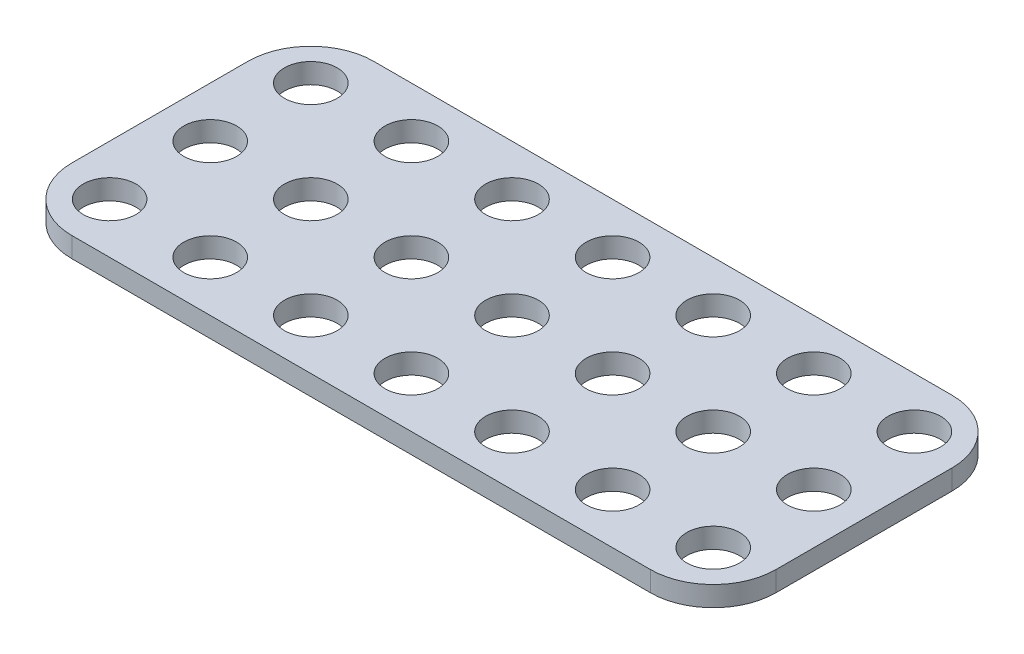
SolidWorks part; units mm, degrees
material "1060 Alloy"
ref_plane "Front Plane" through (0, 0, 0) normal (0, 0, 1) x (1, 0, 0)
ref_plane "Top Plane" through (0, 0, 0) normal (0, 1, 0) x (1, 0, 0)
ref_plane "Right Plane" through (0, 0, 0) normal (1, 0, 0) x (0, 0, -1)
sketch "Sketch1" plane through (0, 0, 0) normal (0, 1, 0) x (1, 0, 0)
  line L1 (0, 0) -> (56, 0)
  line L2 (0, 0) -> (0, -24)
  line L3 (0, -24) -> (56, -24)
  line L4 (56, 0) -> (56, -24)
  dimension "D1" = 24
  dimension "D2" = 56
extrude "Boss-Extrude1" add sketch "Sketch1" along normal blind 1.6
fillet "Fillet1" radius 5 4 edges at (0, 0.8, 0) (56, 0.8, 0) (56, 0.8, 24) (0, 0.8, 24)
sketch "Sketch2" plane through (0, 1.6, 0) normal (0, 1, 0) x (1, 0, 0)
  circle A0 centre (4, -4) radius 2.1
  dimension "D1" = 4.2
  dimension "D2" = 4
  dimension "D3" = 4
extrude "Cut-Extrude1" cut sketch "Sketch2" against normal through all
pattern_linear "LPattern1" count 7 spacing 8 along (1, 0, 0) count 3 spacing 8 along (0, 0, 1) of "Cut-Extrude1"
